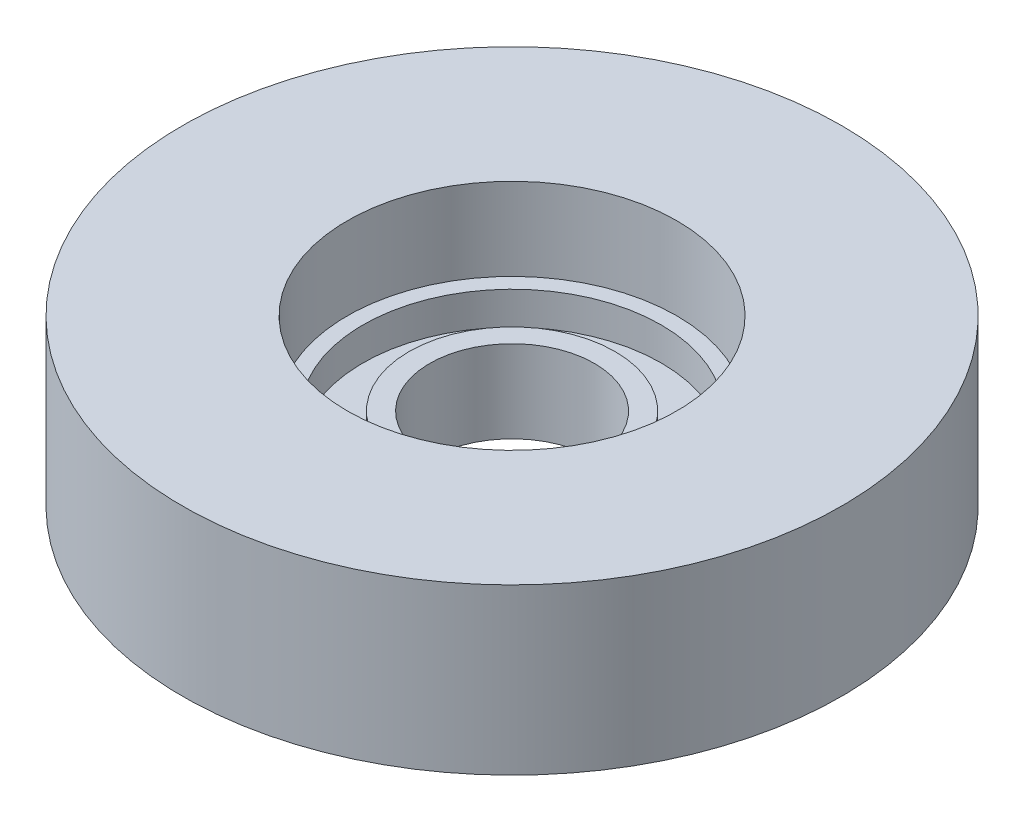
SolidWorks part; units mm, degrees
ref_plane "Front Plane" through (0, 0, 0) normal (0, 0, 1) x (1, 0, 0)
ref_plane "Top Plane" through (0, 0, 0) normal (0, 1, 0) x (1, 0, 0)
ref_plane "Right Plane" through (0, 0, 0) normal (1, 0, 0) x (0, 0, -1)
sketch "Sketch1" plane through (0, 0, 0) normal (0, 0, 1) x (1, 0, 0)
  line L0 (-6.35, 0) -> (-6.35, 6.35)
  line L1 (-11.4935, 6.35) -> (-12.7, 6.35)
  line L2 (-12.7, 6.35) -> (-12.7, 12.7)
  line L3 (-12.7, 12.7) -> (-25.4, 12.7)
  line L4 (-25.4, 12.7) -> (-25.4, 0)
  line L5 (-20.2565, 0) -> (-6.35, 0)
  line L6 (0, 0) -> (0, 10.2706) construction
  line L7 (-11.4935, 6.35) -> (-11.4935, 3.81)
  line L8 (-11.4935, 3.81) -> (-7.9375, 3.81)
  line L9 (-7.9375, 3.81) -> (-7.9375, 6.35)
  line L10 (-7.9375, 6.35) -> (-6.35, 6.35)
  line L11 (-25.4, 0) -> (-23.8125, 0)
  line L12 (-23.8125, 0) -> (-23.8125, 2.54)
  line L13 (-23.8125, 2.54) -> (-20.2565, 2.54)
  line L14 (-20.2565, 2.54) -> (-20.2565, 0)
  dimension "D1" = 6.35
  dimension "D2" = 2.54
  dimension "D3" = 6.35
  dimension "D4" = 6.35
  dimension "D5" = 25.4
  dimension "D6" = 3.556
  dimension "D7" = 6.35
  dimension "D8" = 1.5875
  dimension "D9" = 1.5875
  dimension "D10" = 2.54
  dimension "D11" = 3.556
revolve "Revolve1" add sketch "Sketch1" angle 360 about L6
